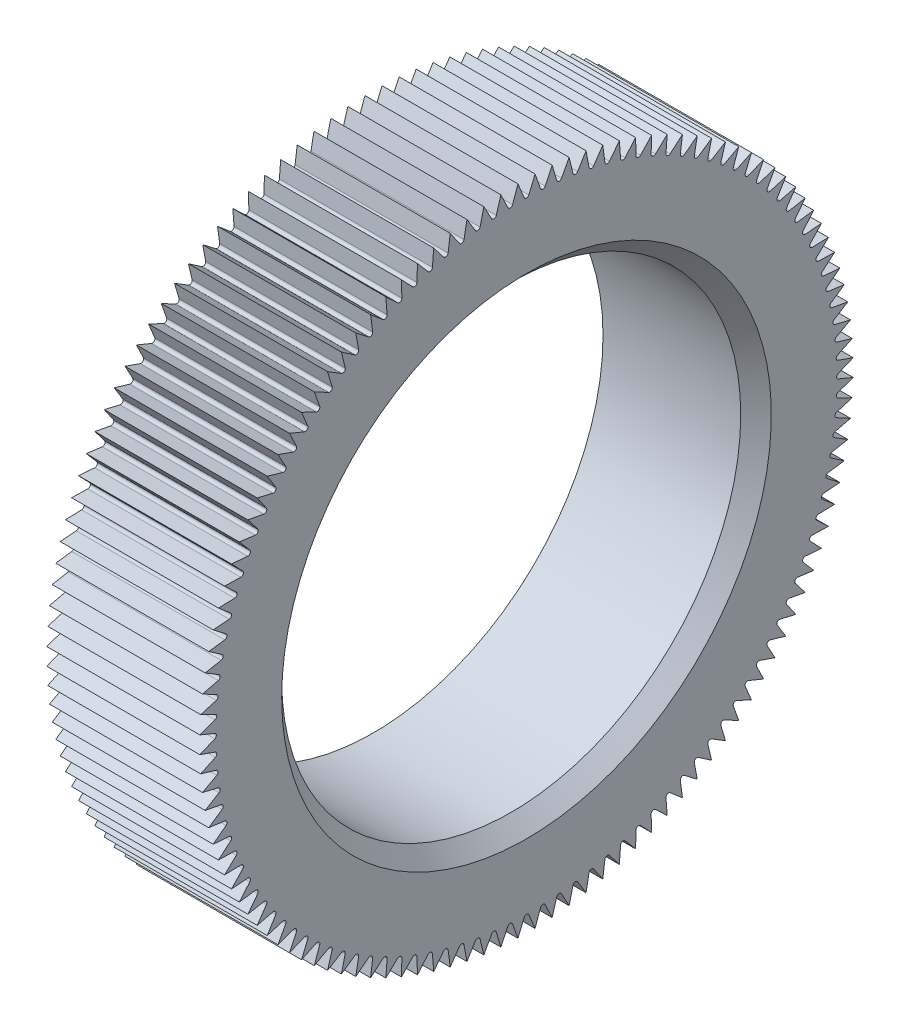
SolidWorks part; units mm, degrees
material "Plain Carbon Steel"
ref_plane "Front " through (0, 0, 0) normal (0, 0, 1) x (1, 0, 0)
ref_plane "Top" through (0, 0, 0) normal (0, 1, 0) x (1, 0, 0)
ref_plane "Right" through (0, 0, 0) normal (1, 0, 0) x (0, 0, -1)
sketch "Sketch1" plane through (0, 0, 0) normal (0, 0, 1) x (1, 0, 0)
  line L0 (0, 0) -> (68.0763, 0) construction
  line L1 (0, 4.5) -> (0, 6.5)
  line L2 (0, 6.5) -> (3, 6.5)
  line L3 (3, 6.5) -> (3, 5.5)
  line L8 (3, 4.5) -> (0, 4.5)
  line L9 (3, 5.5) -> (3, 4.5)
  point P7 (1.5, 4.5)
  dimension "D1" = 2
  dimension "D2" = 3
  dimension "D3" = 1
  dimension "D4" = 4.5
revolve "Revolve1" add sketch "Sketch1" angle 360 about L0
sketch "Sketch2" plane through (3, 0, 0) normal (1, 0, 0) x (0, 0, -1)
  line L0 (0, 0) -> (0, 6) construction
  line L1 (0.0462, 6.1115) -> (0.3107, 6.75)
  line L2 (0.3107, 6.75) -> (-0.3107, 6.75)
  line L3 (-0.3107, 6.75) -> (-0.0462, 6.1115)
  arc A1 (0.0462, 6.1115) -> (-0.0462, 6.1115) centre (0, 6.1307) cw
  dimension "0.1" = 0.05
  dimension "D1" = 0.75
  dimension "D2" = 6
  dimension "D3" = 45
extrude "Cut-Extrude1" cut sketch "Sketch2" against normal through all both and the other way through all
pattern_circular "CirPattern1" count 120 over 360 about axis through (0, 0, 0) along (1, 0, 0) of "Cut-Extrude1"
chamfer "Chamfer1" distance 0.3 angle 45 1 edges at (3, 0, 4.5)
